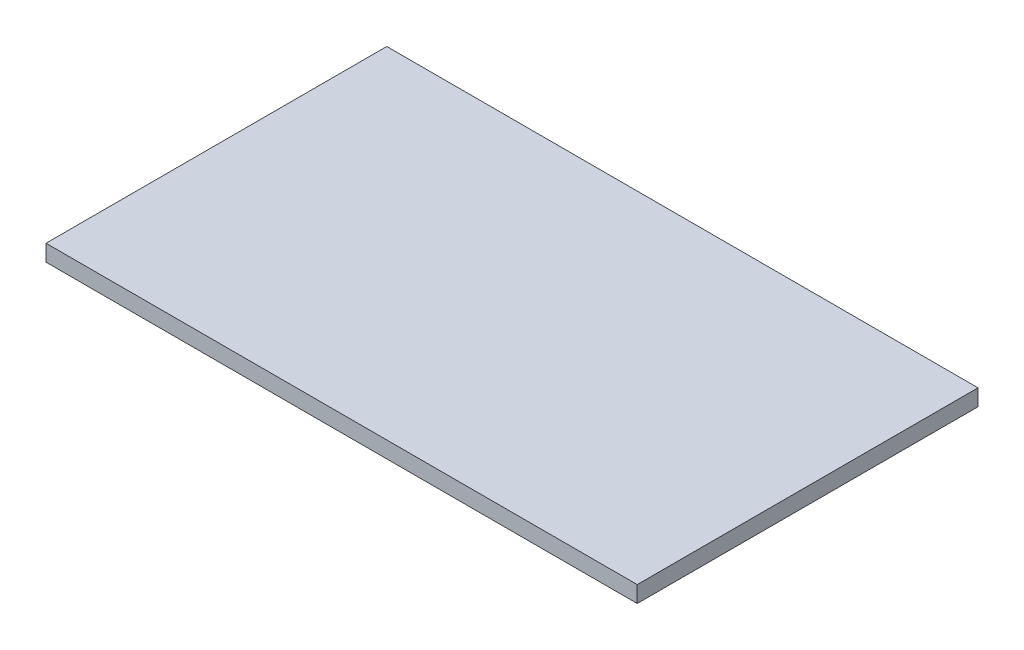
SolidWorks part; units mm, degrees
ref_plane "Front Plane" through (0, 0, 0) normal (0, 0, 1) x (1, 0, 0)
ref_plane "Top Plane" through (0, 0, 0) normal (0, 1, 0) x (1, 0, 0)
ref_plane "Right Plane" through (0, 0, 0) normal (1, 0, 0) x (0, 0, -1)
sketch "Sketch1" plane through (0, 0, 0) normal (0, 1, 0) x (1, 0, 0)
  line L1 (360, -207.5) -> (-360, -207.5)
  line L2 (360, -207.5) -> (360, 207.5)
  line L3 (360, 207.5) -> (-360, 207.5)
  line L4 (-360, -207.5) -> (-360, 207.5)
  line L5 (360, -207.5) -> (-360, 207.5) construction
  line L6 (360, 207.5) -> (-360, -207.5) construction
  point P0 (0, 0)
  dimension "D1" = 720
  dimension "D2" = 415
extrude "Boss-Extrude1" add sketch "Sketch1" along normal mid plane 20
